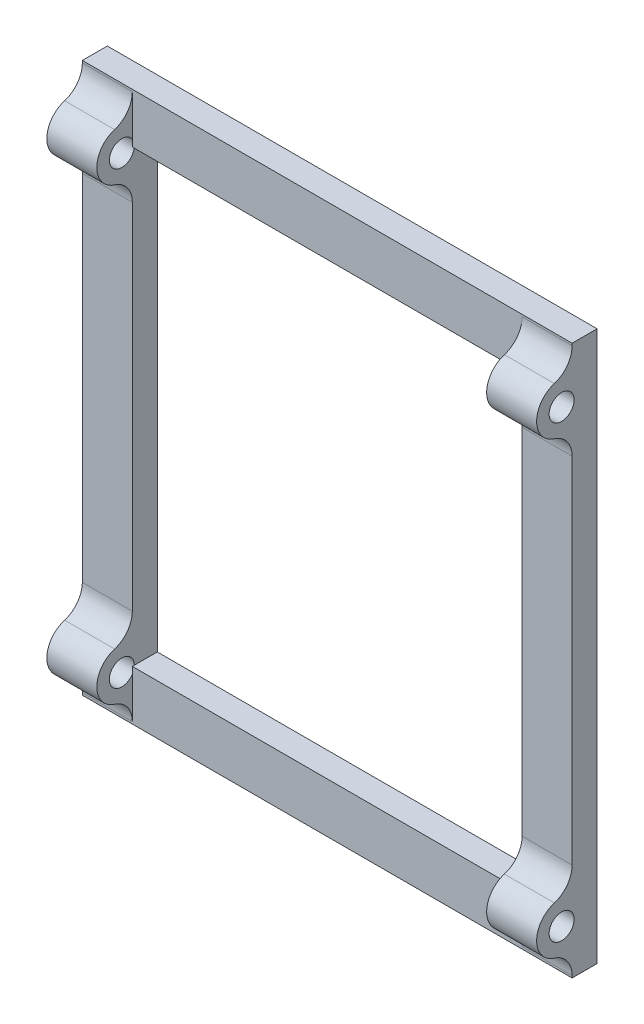
SolidWorks part; units mm, degrees
ref_plane "Plan de face" through (0, 0, 0) normal (0, 0, 1) x (1, 0, 0)
ref_plane "Plan de dessus" through (0, 0, 0) normal (0, 1, 0) x (1, 0, 0)
ref_plane "Plan de droite" through (0, 0, 0) normal (1, 0, 0) x (0, 0, -1)
sketch "Esquisse1" plane through (0, 0, 0) normal (0, 0, 1) x (1, 0, 0)
  line L1 (15.6667, 94.1667) -> (93.6667, 94.1667)
  line L2 (15.6667, 94.1667) -> (15.6667, 4.1667)
  line L3 (15.6667, 4.1667) -> (93.6667, 4.1667)
  line L4 (93.6667, 94.1667) -> (93.6667, 4.1667)
  line L5 (5.6667, 104.1667) -> (103.6667, 104.1667)
  line L6 (5.6667, 104.1667) -> (5.6667, -5.8333)
  line L7 (5.6667, -5.8333) -> (103.6667, -5.8333)
  line L8 (103.6667, 104.1667) -> (103.6667, -5.8333)
  dimension "D1" = 10
  dimension "D2" = 10
  dimension "D3" = 10
  dimension "D4" = 10
  dimension "D5" = 110
  dimension "D6" = 98
extrude "Boss.-Extru.1" add sketch "Esquisse1" along normal blind 5
sketch "Esquisse2" plane through (103.6667, 0, 0) normal (1, 0, 0) x (0, 0, -1)
  line L0 (0, -5.8333) -> (0, 104.1667) construction
  line L1 (-5, 104.1667) -> (0, 104.1667) construction
  circle A0 centre (-7.1, 94.1667) radius 2.5
  circle A1 centre (-7.1, 94.1667) radius 5
  dimension "D1" = 5
  dimension "D2" = 10
  dimension "D3" = 7.1
  dimension "D4" = 10
extrude "Boss.-Extru.2" add sketch "Esquisse2" against normal blind 10
sketch "Esquisse3" plane through (103.6667, 0, 0) normal (1, 0, 0) x (0, 0, -1)
  circle A0 centre (-7.1, 94.1667) radius 2.5
extrude "Enlèv. mat.-Extru.1" cut sketch "Esquisse3" against normal blind 10
pattern_linear "Répétition linéaire3" count 2 spacing 88 along (-1, 0, 0) count 2 spacing 90 along (0, -1, 0) of "Enlèv. mat.-Extru.1", "Boss.-Extru.2"
fillet "Congé1" radius 5 8 edges at (98.6667, 89.629, 5) (98.6667, 98.7043, 5) (10.6667, 89.629, 5) (10.6667, 98.7043, 5) (10.6667, -0.371, 5) (10.6667, 8.7043, 5) (98.6667, -0.371, 5) (98.6667, 8.7043, 5)
